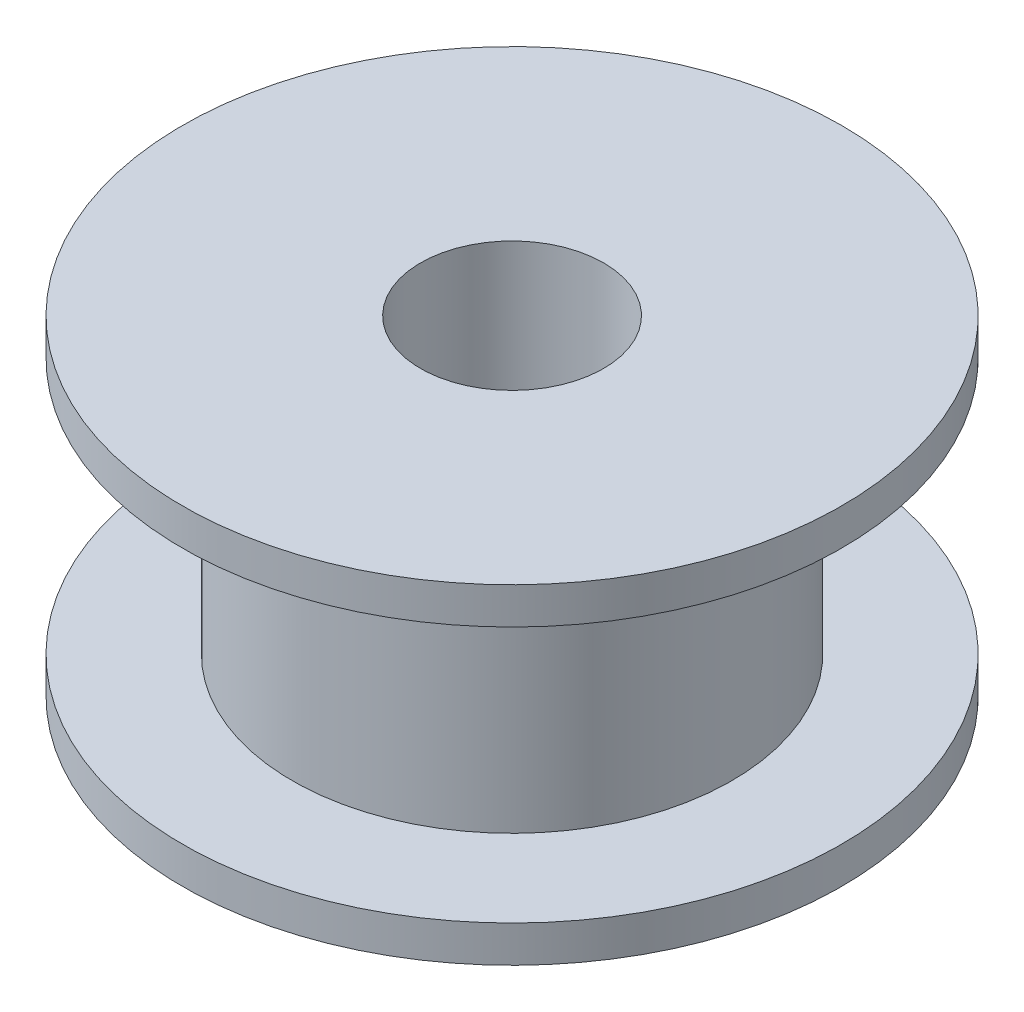
SolidWorks part; units mm, degrees
material "Plain Carbon Steel"
ref_plane "Front Plane" through (0, 0, 0) normal (0, 0, 1) x (1, 0, 0)
ref_plane "Top Plane" through (0, 0, 0) normal (0, 1, 0) x (1, 0, 0)
ref_plane "Right Plane" through (0, 0, 0) normal (1, 0, 0) x (0, 0, -1)
sketch "Sketch1" plane through (0, 0, 0) normal (0, 0, 1) x (1, 0, 0)
  line L0 (0, 0) -> (0, 20.3477) construction
  line L1 (2.5, -4.5) -> (2.5, 4.5)
  line L2 (9, 4.5) -> (9, 3.5)
  line L3 (9, 3.5) -> (6, 3.5)
  line L4 (6, 3.5) -> (6, -3.5)
  line L5 (2.5, 4.5) -> (9, 4.5)
  line L6 (0, 0) -> (6, 0) construction
  line L7 (9, -3.5) -> (6, -3.5)
  line L8 (9, -4.5) -> (9, -3.5)
  line L9 (2.5, -4.5) -> (9, -4.5)
  point P13 (2.5, 0)
  dimension "D1" = 5
  dimension "D2" = 12
  dimension "D3" = 18
  dimension "D4" = 9
  dimension "D5" = 7
revolve "Revolve1" add sketch "Sketch1" angle 360 about L0
